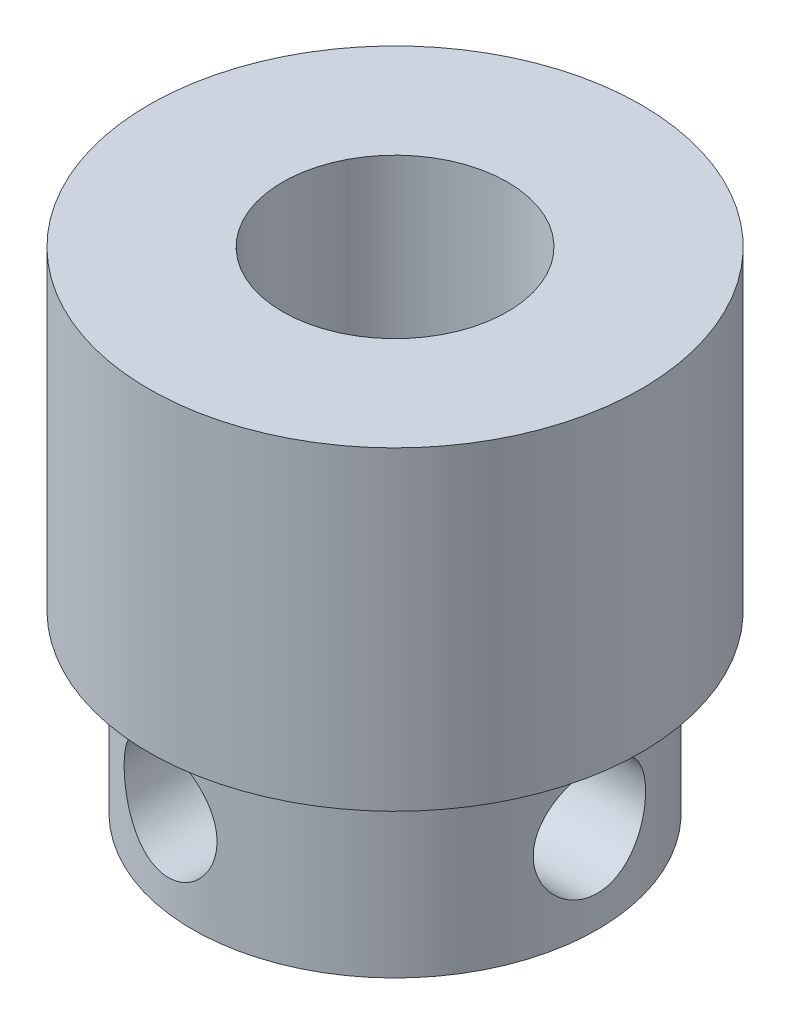
SolidWorks part; units mm, degrees
ref_plane "Front Plane" through (0, 0, 0) normal (0, 0, 1) x (1, 0, 0)
ref_plane "Top Plane" through (0, 0, 0) normal (0, 1, 0) x (1, 0, 0)
ref_plane "Right Plane" through (0, 0, 0) normal (1, 0, 0) x (0, 0, -1)
ref_plane "Plane1" through (0, 0, -56.4) normal (0, 0, 1) x (1, 0, 0)
sketch "Sketch1" plane through (0, 0, -56.4) normal (0, 0, 1) x (1, 0, 0)
  line L0 (80.975, 56.4264) -> (75.5, 56.4264)
  line L1 (75.5, 56.4264) -> (75.5, 49.4264)
  line L2 (75.5, 49.4264) -> (80.975, 49.4264)
  line L3 (80.975, 49.4264) -> (80.975, 56.4264)
  line L4 (75.5, 56.4264) -> (75.5, 49.4264) construction
revolve "Revolve1" add sketch "Sketch1" angle 360 about L4
sketch "Sketch2" plane through (0, 49.4264, 0) normal (0, -1, 0) x (1, 0, 0)
  circle A0 centre (75.5, -56.4) radius 4.5
extrude "Boss-Extrude1" add sketch "Sketch2" along normal blind 3.9
hole_wizard "Ø5.0 (5) Diameter Hole1" positions "Sketch4" profile "Sketch3" hole size "Ø5.0" standard "ANSI Metric"
sketch "Sketch4" plane through (0, 56.4264, 0) normal (0, 1, 0) x (1, 0, 0)
  point P0 (75.5, 56.4)
sketch "Sketch3" plane through (75.5, 56.4264, -56.4) normal (1, 0, 0) x (0, 0, 1)
  line L0 (0, 0) -> (0, 10.9)
  line L1 (0, 10.9) -> (2.5, 10.9)
  line L2 (2.5, 10.9) -> (2.5, 0)
  line L5 (2.5, 0) -> (0, 0)
  line L11 (0, -6.35) -> (0, 107.95) construction
  dimension "Thru Hole Dia." = 5
  dimension "Thru Hole Depth" = 10.9
ref_plane "Plane2" through (77.6651, 0, 0) normal (-1, 0, 0) x (0, 0, 1)
hole_wizard "Ø2.5 (2.5) Diameter Hole1" positions "Sketch6" profile "Sketch5" hole size "Ø2.5" standard "ANSI Metric"
sketch "Sketch6" plane through (77.6651, 0, 0) normal (-1, 0, 0) x (0, 0, 1)
  point P0 (-56.4, 47.4764)
sketch "Sketch5" plane through (77.6651, 47.4764, -56.4) normal (0, 1, 0) x (0, 0, 1)
  line L0 (0, 0) -> (0, 3.3099)
  line L1 (0, 3.3099) -> (1.25, 3.3099)
  line L2 (1.25, 3.3099) -> (1.25, 0)
  line L5 (1.25, 0) -> (0, 0)
  line L11 (0, -6.35) -> (0, 107.95) construction
  dimension "Thru Hole Dia." = 2.5
  dimension "Thru Hole Depth" = 3.3099
ref_plane "Plane3" through (0, 0, -54.8854) normal (0, 0, -1) x (-1, 0, 0)
hole_wizard "Ø2.5 (2.5) Diameter Hole2" positions "Sketch8" profile "Sketch7" hole size "Ø2.5" standard "ANSI Metric"
sketch "Sketch8" plane through (0, 0, -54.8854) normal (0, 0, -1) x (-1, 0, 0)
  point P0 (-74.761, 47.4594)
sketch "Sketch7" plane through (74.761, 47.4594, -54.8854) normal (1, 0, 0) x (0, 1, 0)
  line L0 (0, 0) -> (0, 3.9604)
  line L1 (0, 3.9604) -> (1.25, 3.9604)
  line L2 (1.25, 3.9604) -> (1.25, 0)
  line L5 (1.25, 0) -> (0, 0)
  line L11 (0, -6.35) -> (0, 107.95) construction
  dimension "Thru Hole Dia." = 2.5
  dimension "Thru Hole Depth" = 3.9604
